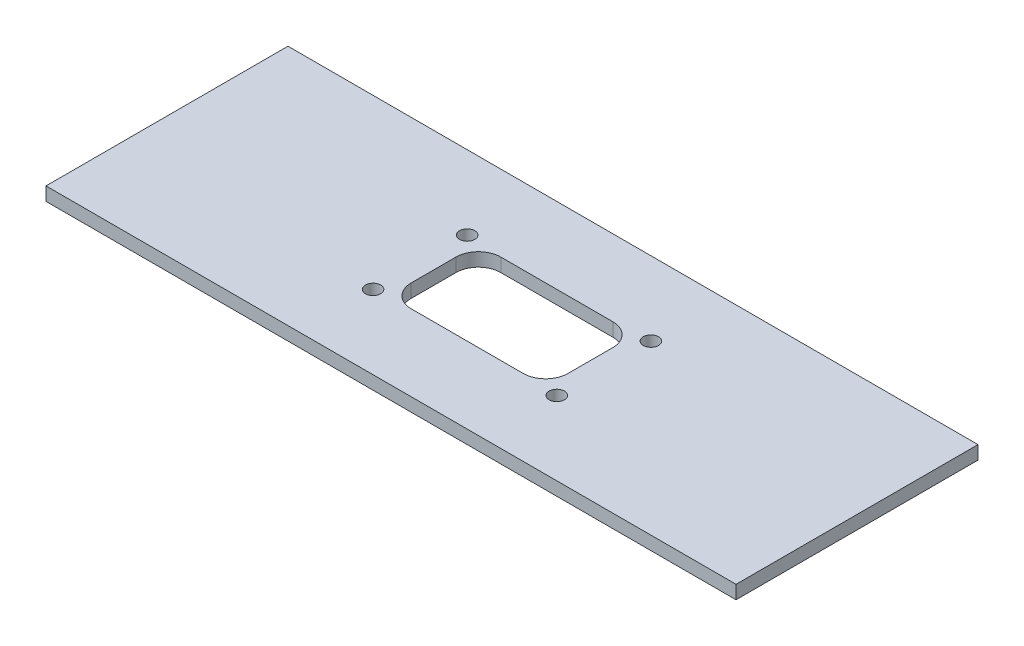
SolidWorks part; units mm, degrees
material "Plain Carbon Steel"
ref_plane "Front Plane" through (0, 0, 0) normal (0, 0, 1) x (1, 0, 0)
ref_plane "Top Plane" through (0, 0, 0) normal (0, 1, 0) x (1, 0, 0)
ref_plane "Right Plane" through (0, 0, 0) normal (1, 0, 0) x (0, 0, -1)
sketch "Sketch1" plane through (0, 0, 0) normal (0, 1, 0) x (1, 0, 0)
  line L1 (-154, -54) -> (154, -54)
  line L2 (-154, -54) -> (-154, 54)
  line L3 (-154, 54) -> (154, 54)
  line L4 (154, -54) -> (154, 54)
  line L5 (-154, -54) -> (154, 54) construction
  line L6 (-154, 54) -> (154, -54) construction
  point P0 (0, 0)
  dimension "D1" = 108
  dimension "D2" = 308
extrude "Boss-Extrude1" add sketch "Sketch1" along normal blind 6
sketch "Sketch2" plane through (0, 0, 0) normal (0, -1, 0) x (1, 0, 0)
  line L1 (-25, -20) -> (25, -20)
  line L2 (-35, -10) -> (-35, 10)
  line L3 (-25, 20) -> (25, 20)
  line L4 (35, -10) -> (35, 10)
  line L5 (-35, -20) -> (35, 20) construction
  line L6 (-35, 20) -> (35, -20) construction
  arc A0 (-35, 10) -> (-25, 20) centre (-25, 10) cw
  arc A1 (-25, -20) -> (-35, -10) centre (-25, -10) cw
  arc A2 (25, -20) -> (35, -10) centre (25, -10) ccw
  arc A3 (25, 20) -> (35, 10) centre (25, 10) cw
  point P0 (0, 0)
  dimension "D3" = 10
  dimension "D1" = 40
  dimension "D2" = 70
extrude "Cut-Extrude1" cut sketch "Sketch2" against normal blind 10
sketch "Sketch3" plane through (0, 0, 0) normal (0, -1, 0) x (-1, 0, 0)
  line L1 (50, 30) -> (-50, 30) construction
  line L2 (50, 30) -> (50, -30) construction
  line L3 (50, -30) -> (-50, -30) construction
  line L4 (-50, 30) -> (-50, -30) construction
  line L8 (0, -30) -> (0, 30) construction
  line L9 (50, 0) -> (-50, 0) construction
  circle A0 centre (41, -21) radius 3.4
  circle A3 centre (-41, -21) radius 3.4
  circle A4 centre (-41, 21) radius 3.4
  circle A5 centre (41, 21) radius 3.4
  point P0 (0, 0)
  dimension "D7" = 6.8
  dimension "D1" = 60
  dimension "D2" = 100
  dimension "D3" = 50
  dimension "D4" = 30
  dimension "D5" = 9
  dimension "D6" = 9
extrude "Cut-Extrude2" cut sketch "Sketch3" against normal through all
cosmetic thread "Cosmetic Thread1" parameters "D2"=8
cosmetic thread "Cosmetic Thread2" parameters "D2"=8
cosmetic thread "Cosmetic Thread3" parameters "D2"=8
cosmetic thread "Cosmetic Thread4" parameters "D2"=8
